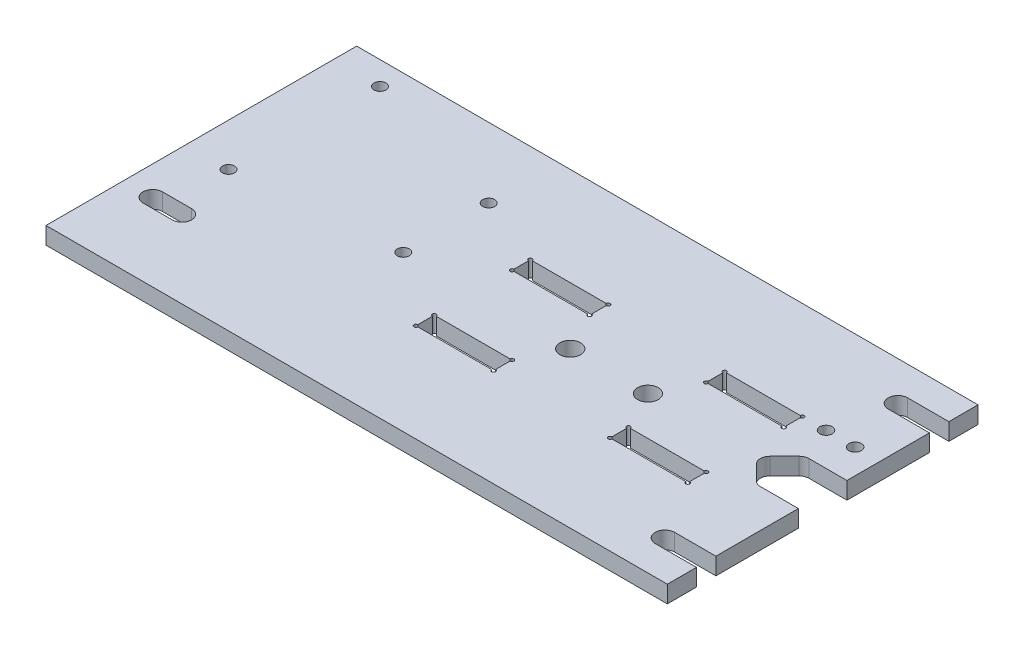
SolidWorks part; units mm, degrees
material "Acrylic (Medium-high impact)"
ref_plane "Front Plane" through (0, 0, 0) normal (0, 0, 1) x (1, 0, 0)
ref_plane "Top Plane" through (0, 0, 0) normal (0, 1, 0) x (1, 0, 0)
ref_plane "Right Plane" through (0, 0, 0) normal (1, 0, 0) x (0, 0, -1)
sketch "Sketch1" plane through (0, 0, 0) normal (0, 1, 0) x (1, 0, 0)
  line L0 (0, 11.3076) -> (0, -10.8315) construction
  line L1 (-101.6, 50.8) -> (101.6, 50.8)
  line L2 (-101.6, 50.8) -> (-101.6, -50.8)
  line L3 (-101.6, -50.8) -> (101.6, -50.8)
  line L4 (101.6, 50.8) -> (101.6, 7.9375)
  line L5 (-101.6, 50.8) -> (101.6, -50.8) construction
  line L6 (-101.6, -50.8) -> (101.6, 50.8) construction
  line L7 (-24.7577, 0) -> (22.1391, 0) construction
  line L8 (86.9273, 7.0076) -> (82.1648, 2.2451)
  line L9 (86.9273, -7.0076) -> (82.1648, -2.2451)
  line L10 (101.6, 0) -> (112.1126, 0) construction
  line L11 (101.6, -7.9375) -> (101.6, -50.8)
  line L12 (89.1724, 7.9375) -> (101.6, 7.9375)
  line L13 (89.1724, -7.9375) -> (101.6, -7.9375)
  circle A0 centre (-88.9, 38.1) radius 3.175 construction
  circle A1 centre (88.9, 38.1) radius 3.175 construction
  circle A2 centre (-88.9, -38.1) radius 3.175 construction
  circle A3 centre (88.9, -38.1) radius 3.175 construction
  circle A4 centre (88.9, 0) radius 3.175 construction
  circle A5 centre (88.9, 0) radius 6.35 construction
  arc A6 (82.1648, 2.2451) -> (82.1648, -2.2451) centre (84.4099, 0) ccw
  arc A7 (86.9273, -7.0076) -> (89.1724, -7.9375) centre (89.1724, -4.7625) ccw
  arc A8 (89.1724, 7.9375) -> (86.9273, 7.0076) centre (89.1724, 4.7625) ccw
  point P0 (0, 0)
  point P28 (79.9197, 0)
  point P33 (87.8572, -7.9375)
  point P36 (87.8572, 7.9375)
  dimension "D3" = 6.35
  dimension "D6" = 12.7
  dimension "D7" = 3.175
  dimension "D9" = 3.175
  dimension "D1" = 203.2
  dimension "D2" = 101.6
  dimension "D4" = 12.7
  dimension "D5" = 12.7
  dimension "D8" = 15.875
extrude "Boss-Extrude1" add sketch "Sketch1" along normal blind 5.588
hole_wizard "1/4 Clearance Hole1" positions "Sketch3" profile "Sketch2" hole size "1/4" standard "Ansi Inch" end condition up to next
sketch "Sketch3" plane through (0, 5.588, 0) normal (0, 1, 0) x (-1, 0, 0)
  line L0 (-101.6, -50.8) -> (101.6, -50.8) construction
  point P3 (-88.1062, 38.1)
  point P6 (-88.1062, -38.1)
  point P12 (88.9, 25.4)
  dimension "D1" = 76.2
  dimension "D2" = 0.7937
sketch "Sketch2" plane through (88.1062, 5.588, 38.1) normal (1, 0, 0) x (0, 0, 1)
  line L0 (0, 0) -> (0, 5.588)
  line L1 (0, 5.588) -> (3.175, 5.588)
  line L2 (3.175, 5.588) -> (3.175, 0)
  line L5 (3.175, 0) -> (0, 0)
  line L11 (0, -6.35) -> (0, 107.95) construction
  dimension "Thru Hole Dia." = 6.35
  dimension "Thru Hole Depth" = 5.588
sketch "Sketch4" plane through (0, 5.588, 0) normal (0, 1, 0) x (1, 0, 0)
  line L0 (88.1062, 41.275) -> (101.6, 41.275)
  line L1 (101.6, 7.9375) -> (101.6, 50.8) construction
  line L2 (88.1062, 34.925) -> (101.6, 34.925)
  line L3 (101.6, 34.925) -> (101.6, 41.275)
  circle A0 centre (88.1062, 38.1) radius 3.175 construction
  arc A1 (88.1062, 41.275) -> (88.1062, 34.925) centre (88.1062, 38.1) ccw
extrude "Cut-Extrude1" cut sketch "Sketch4" against normal up to next (5.588 mm away)
mirror "Mirror1" about plane through (0, 0, 0) normal (0, 0, 1) of "Cut-Extrude1"
sketch "Sketch5" plane through (0, 5.588, 0) normal (0, 1, 0) x (1, 0, 0)
  line L0 (-92.075, -25.4) -> (-88.9, -25.4) construction
  line L1 (-92.075, -22.225) -> (-88.9, -22.225)
  line L2 (-92.075, -28.575) -> (-88.9, -28.575)
  arc A0 (-92.075, -22.225) -> (-92.075, -28.575) centre (-92.075, -25.4) ccw
  arc A1 (-88.9, -28.575) -> (-88.9, -22.225) centre (-88.9, -25.4) ccw
  circle A3 centre (-88.9, -25.4) radius 3.175 construction
  point P3 (-90.4875, -25.4)
  dimension "D1" = 3.175
extrude "Cut-Extrude2" cut sketch "Sketch5" against normal up to next
sketch "Sketch6" plane through (0, 5.588, 0) normal (0, 1, 0) x (1, 0, 0)
  line L0 (-101.6, 45.72) -> (-101.6, -7.62)
  line L1 (-101.6, -7.62) -> (-33.02, -7.62)
  line L2 (-33.02, -7.62) -> (-33.02, 33.02)
  line L3 (-33.02, 33.02) -> (-35.56, 33.02)
  line L4 (-35.56, 33.02) -> (-35.56, 45.72)
  line L5 (-35.56, 45.72) -> (-101.6, 45.72)
  line L6 (-101.6, 50.8) -> (-101.6, -50.8) construction
  line L7 (101.6, 50.8) -> (-101.6, 50.8) construction
  point P0 (-86.36, 43.18)
  point P1 (-35.56, 27.94)
  point P2 (-35.56, 0)
  point P3 (-87.63, -5.08)
  dimension "D1" = 50.8
  dimension "D2" = 15.24
  dimension "D3" = 27.94
  dimension "D4" = 5.08
  dimension "D5" = 50.8
  dimension "D6" = 13.97
  dimension "D7" = 68.58
  dimension "D8" = 2.54
  dimension "D9" = 53.34
  dimension "D10" = 5.08
  dimension "D11" = 5.08
  dimension "D12" = 1.27
hole_wizard "#4 Clearance Hole1" positions "Sketch8" profile "Sketch7" hole size "#4" standard "Ansi Inch" end condition up to next
sketch "Sketch8" plane through (0, 5.588, 0) normal (0, 1, 0) x (-1, 0, 0)
  point P0 (86.36, -43.18)
  point P1 (35.56, -27.94)
  point P4 (35.56, 0)
  point P7 (87.63, 5.08)
sketch "Sketch7" plane through (-86.36, 5.588, -43.18) normal (1, 0, 0) x (0, 0, 1)
  line L0 (0, 0) -> (0, 5.588)
  line L1 (0, 5.588) -> (1.9685, 5.588)
  line L2 (1.9685, 5.588) -> (1.9685, 0)
  line L5 (1.9685, 0) -> (0, 0)
  line L11 (0, -6.35) -> (0, 107.95) construction
  dimension "Thru Hole Dia." = 3.937
  dimension "Thru Hole Depth" = 5.588
sketch "Sketch9" plane through (0, 5.588, 0) normal (0, 1, 0) x (1, 0, 0)
  line L0 (0, 0) -> (51.0478, 0) construction
  line L1 (31.75, 21.6464) -> (31.75, -6.4609) construction
  line L2 (-6.0325, 18.7198) -> (6.0325, 18.7198)
  line L3 (-6.35, 18.4023) -> (-6.35, 13.0175) construction
  line L4 (-6.0325, 12.7) -> (6.0325, 12.7)
  line L5 (6.35, 18.4023) -> (6.35, 13.0175) construction
  line L6 (-6.35, 18.7198) -> (6.35, 12.7) construction
  line L7 (-6.35, 12.7) -> (6.35, 18.7198) construction
  line L8 (69.85, 12.7) -> (57.15, 18.7198) construction
  line L9 (69.85, 18.7198) -> (57.15, 12.7) construction
  line L10 (57.15, 18.4023) -> (57.15, 13.0175) construction
  line L11 (69.5325, 12.7) -> (57.4675, 12.7)
  line L12 (69.85, 18.4023) -> (69.85, 13.0175) construction
  line L13 (69.5325, 18.7198) -> (57.4675, 18.7198)
  line L14 (57.4675, 18.7198) -> (57.15, 18.7198)
  line L15 (57.15, 18.7198) -> (57.15, 18.4023) construction
  line L16 (69.5325, 18.7198) -> (69.85, 18.7198)
  line L17 (69.85, 18.7198) -> (69.85, 18.4023) construction
  line L18 (69.85, 13.0175) -> (69.85, 12.7) construction
  line L19 (69.85, 12.7) -> (69.5325, 12.7)
  line L20 (57.4675, 12.7) -> (57.15, 12.7)
  line L21 (57.15, 12.7) -> (57.15, 13.0175) construction
  line L22 (-6.35, 18.4023) -> (-6.35, 18.7198) construction
  line L23 (-6.35, 18.7198) -> (-6.0325, 18.7198)
  line L24 (6.0325, 18.7198) -> (6.35, 18.7198)
  line L25 (6.35, 18.7198) -> (6.35, 18.4023) construction
  line L26 (6.35, 13.0175) -> (6.35, 12.7) construction
  line L27 (6.35, 12.7) -> (6.0325, 12.7)
  line L28 (-6.0325, 12.7) -> (-6.35, 12.7)
  line L29 (-6.35, 12.7) -> (-6.35, 13.0175) construction
  line L30 (6.35, 18.7198) -> (12.7, 18.7198)
  line L31 (12.7, 12.7) -> (6.35, 12.7)
  line L32 (12.7, 18.7198) -> (12.7, 12.7)
  line L33 (-6.35, 18.7198) -> (-12.7, 18.7198)
  line L34 (-12.7, 18.7198) -> (-12.7, 12.7)
  line L35 (-12.7, 12.7) -> (-6.35, 12.7)
  line L36 (69.85, 18.7198) -> (76.2, 18.7198)
  line L37 (76.2, 18.7198) -> (76.2, 12.7)
  line L38 (76.2, 12.7) -> (69.85, 12.7)
  line L39 (50.8, 12.7) -> (57.15, 12.7)
  line L40 (50.8, 18.7198) -> (50.8, 12.7)
  line L41 (57.15, 18.7198) -> (50.8, 18.7198)
  arc A0 (-6.0325, 18.7198) -> (-6.35, 18.4023) centre (-6.35, 18.7198) ccw construction
  arc A1 (6.35, 18.4023) -> (6.0325, 18.7198) centre (6.35, 18.7198) ccw construction
  arc A2 (6.0325, 12.7) -> (6.35, 13.0175) centre (6.35, 12.7) ccw construction
  arc A3 (-6.35, 13.0175) -> (-6.0325, 12.7) centre (-6.35, 12.7) ccw construction
  arc A4 (69.85, 13.0175) -> (69.5325, 12.7) centre (69.85, 12.7) cw construction
  arc A5 (57.4675, 12.7) -> (57.15, 13.0175) centre (57.15, 12.7) cw construction
  arc A6 (57.15, 18.4023) -> (57.4675, 18.7198) centre (57.15, 18.7198) cw construction
  arc A7 (69.5325, 18.7198) -> (69.85, 18.4023) centre (69.85, 18.7198) cw construction
  point P4 (0, 15.7099)
  point P30 (63.5, 15.7099)
  point P31 (31.75, 0)
  dimension "D6" = 0.635
  dimension "D7" = 6.35
  dimension "D1" = 25.4
  dimension "D2" = 25.4
  dimension "D3" = 12.7
  dimension "D4" = 6.0198
  dimension "D5" = 63.5
  dimension "D8" = 6.35
extrude "Cut-Extrude3" cut sketch "Sketch9" against normal up to next (5.588 mm away)
sketch "Sketch15" plane through (0, 5.588, 0) normal (0, 1, 0) x (1, 0, 0)
  line L0 (-12.7, 12.7) -> (12.7, 12.7) construction
  circle A0 centre (-12.7, 18.7198) radius 0.635
  circle A1 centre (12.7, 18.7198) radius 0.635
  circle A2 centre (12.7, 12.7) radius 0.635
  circle A3 centre (-12.7, 12.7) radius 0.635
  dimension "D1" = 1.27
extrude "Cut-Extrude5" cut sketch "Sketch15" against normal up to next (5.588 mm away)
ref_plane "Plane1" through (31.75, 0, 0) normal (-1, 0, 0) x (0, 0, 1)
mirror "Mirror3" about plane through (31.75, 0, 0) normal (-1, 0, 0) of "Cut-Extrude5"
mirror "Mirror2" about plane through (0, 0, 0) normal (0, 0, 1) of "Mirror3", "Cut-Extrude3", "Cut-Extrude5"
hole_wizard "#10 Clearance Hole1" positions "Sketch11" profile "Sketch10" hole size "#10" standard "ANSI Inch" end condition up to next
sketch "Sketch11" plane through (0, 5.588, 0) normal (0, 1, 0) x (-1, 0, 0)
  line L1 (0, 0) -> (-51.0478, 0) construction
  line L2 (-44.45, 0) -> (-19.05, 0) construction
  line L3 (-12.065, 18.7198) -> (12.065, 18.7198) construction
  line L4 (-75.565, 18.7198) -> (-51.435, 18.7198) construction
  line L5 (-63.5, 18.7198) -> (0, 18.7198) construction
  line L7 (-31.75, 0) -> (-31.75, 18.7198) construction
  point P0 (-19.05, 0)
  point P37 (-44.45, 0)
  dimension "D1" = 25.4
sketch "Sketch10" plane through (19.05, 5.588, 0) normal (1, 0, 0) x (0, 0, 1)
  line L0 (0, 0) -> (0, 5.588)
  line L1 (0, 5.588) -> (3.3909, 5.588)
  line L2 (3.3909, 5.588) -> (3.3909, 0)
  line L5 (3.3909, 0) -> (0, 0)
  line L11 (0, -6.35) -> (0, 107.95) construction
  dimension "Thru Hole Dia." = 6.7818
  dimension "Thru Hole Depth" = 5.588
hole_wizard "Tap Drill for #4 Helicoil1" positions "Sketch13" profile "Sketch12" hole size "#4-40" standard "ANSI Inch"
sketch "Sketch13" plane through (0, 5.588, 0) normal (0, 1, 0) x (1, 0, 0)
  line L0 (89.1724, 7.9375) -> (101.6, 7.9375) construction
  line L1 (101.6, 7.9375) -> (101.6, 34.925) construction
  point P0 (93.4847, 18.7325)
  point P2 (83.9597, 18.7325)
  dimension "D1" = 10.795
  dimension "D2" = 9.525
  dimension "D3" = 8.1153
sketch "Sketch12" plane through (93.4847, 5.588, -18.7325) normal (1, 0, 0) x (0, 0, 1)
  line L0 (0, 0) -> (0, 7.5709)
  line L1 (0, 7.5709) -> (2.032, 6.35)
  line L2 (2.032, 6.35) -> (2.032, 0)
  line L5 (2.032, 0) -> (0, 0)
  line L10 (0, 7.5709) -> (-2.032, 6.35) construction
  line L11 (0, -6.35) -> (0, 107.95) construction
  dimension "Hole Dia." = 4.064
  dimension "Hole Depth" = 6.35
  dimension "Drill Angle" = 118
sketch "Sketch14" plane through (0, 5.588, 0) normal (0, 1, 0) x (1, 0, 0)
  line L0 (-88.9, -22.225) -> (-82.55, -22.225)
  line L1 (-82.55, -28.575) -> (-88.9, -28.575)
  arc A0 (-82.55, -22.225) -> (-82.55, -28.575) centre (-82.55, -25.4) cw
  arc A1 (-88.9, -28.575) -> (-88.9, -22.225) centre (-88.9, -25.4) ccw construction
  arc A2 (-88.9, -28.575) -> (-88.9, -22.225) centre (-88.9, -25.4) ccw
  dimension "D1" = 6.35
extrude "Cut-Extrude4" cut sketch "Sketch14" against normal up to next
